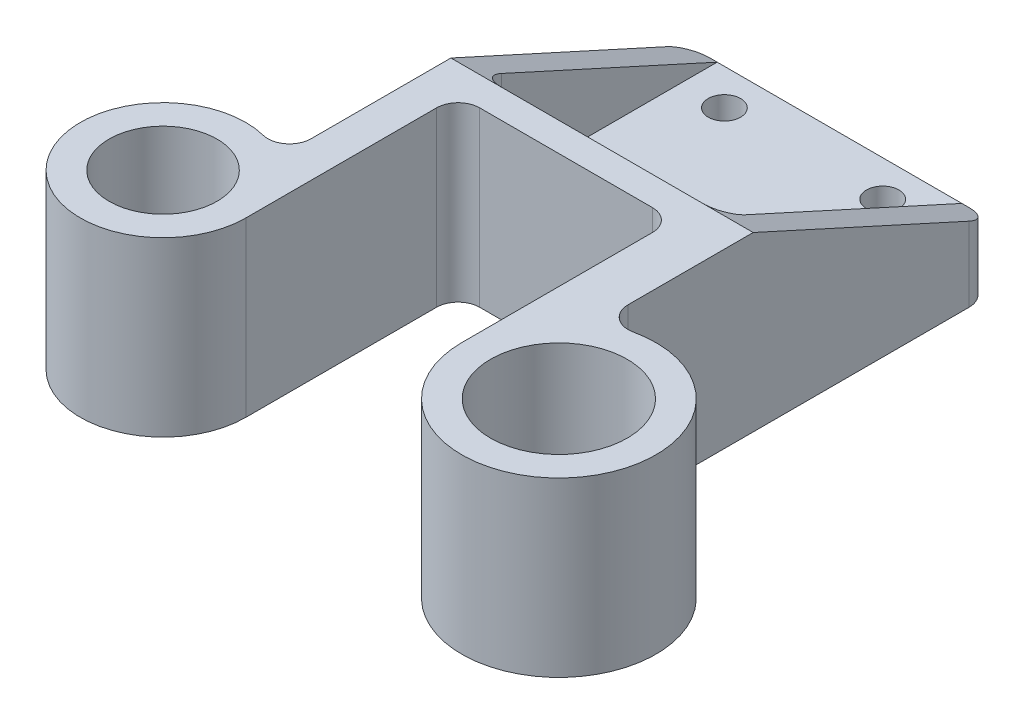
SolidWorks part; units mm, degrees
ref_plane "Front Plane" through (0, 0, 0) normal (0, 0, 1) x (1, 0, 0)
ref_plane "Top Plane" through (0, 0, 0) normal (0, 1, 0) x (1, 0, 0)
ref_plane "Right Plane" through (0, 0, 0) normal (1, 0, 0) x (0, 0, -1)
sketch "Sketch1" plane through (0, 0, 0) normal (0, 1, 0) x (1, 0, 0)
  line L0 (-27.5, 0) -> (27.5, 0) construction
  line L1 (21, 33.5) -> (21, 11.8322)
  line L2 (-11, 38.5) -> (11, 38.5)
  line L3 (-11, 38.5) -> (-11, 61.5)
  line L4 (-11, 61.5) -> (11, 61.5)
  line L5 (11, 38.5) -> (11, 61.5)
  line L6 (-11, 38.5) -> (11, 61.5) construction
  line L7 (-11, 61.5) -> (11, 38.5) construction
  line L8 (-21, 33.5) -> (21, 33.5)
  line L9 (-21, 33.5) -> (-21, 66.5)
  line L10 (-21, 66.5) -> (21, 66.5)
  line L11 (21, 33.5) -> (21, 66.5)
  line L12 (-21, 33.5) -> (21, 66.5) construction
  line L13 (-21, 66.5) -> (21, 33.5) construction
  line L14 (14, 0) -> (14, 33.5)
  line L15 (-16, 0) -> (-16, 33.5)
  line L16 (-21, 33.5) -> (-21, 9.4868)
  line L17 (-16, 29.5) -> (14, 29.5)
  circle A0 centre (27.5, 0) radius 9.5
  circle A1 centre (-27.5, 0) radius 7.5
  circle A2 centre (27.5, 0) radius 13.5
  circle A3 centre (-27.5, 0) radius 11.5
  circle A4 centre (-11, 61.5) radius 2.25
  circle A5 centre (11, 61.5) radius 2.25
  circle A6 centre (11, 38.5) radius 2.25
  circle A7 centre (-11, 38.5) radius 2.25
  point P7 (0, 50)
  point P16 (0, 50)
  dimension "D1" = 15
  dimension "D2" = 19
  dimension "D4" = 4
  dimension "D5" = 4
  dimension "D8" = 4.5
  dimension "D9" = 4.5
  dimension "D10" = 4.5
  dimension "D11" = 4.5
  dimension "D3" = 55
  dimension "D6" = 23
  dimension "D7" = 22
  dimension "D12" = 10
  dimension "D13" = 5
  dimension "D14" = 50
  dimension "D15" = 4
extrude "Boss-Extrude1" add sketch "Sketch1" along normal blind 24 contours A3 A1 | A3 L15 L8 L16 | L8 L11 L10 L9 A7 L3 A4 L4 A5 L5 A6 L2 | A2 A0 | A7 L2 A6 L5 A5 L4 A4 L3 | A2 L1 L8 L14 | L15 L17 L14 L8
sketch "Sketch2" plane through (0, 24, 0) normal (0, 1, 0) x (1, 0, 0)
  line L0 (-21, 66.5) -> (21, 66.5) construction
  line L1 (-17, 66.5) -> (17, 66.5)
  line L2 (-17, 66.5) -> (-17, 33.5)
  line L3 (-17, 33.5) -> (17, 33.5)
  line L4 (17, 66.5) -> (17, 33.5)
  line L5 (-16, 29.5) -> (14, 29.5) construction
  line L6 (-21, 9.4868) -> (-21, 66.5) construction
  line L7 (21, 66.5) -> (21, 11.8322) construction
  dimension "D1" = 4
  dimension "D2" = 4
  dimension "D3" = 4
extrude "Cut-Extrude1" cut sketch "Sketch2" against normal blind 15
sketch "Sketch4" plane through (-17, 0, 0) normal (1, 0, 0) x (0, 0, -1)
  line L0 (33.5, 24) -> (66.5, 9)
  line L1 (66.5, 9) -> (66.5, 24)
  line L2 (66.5, 24) -> (33.5, 24) construction
  line L3 (66.5, 9) -> (66.5, 24) construction
  line L4 (66.5, 24) -> (33.5, 24)
extrude "Cut-Extrude2" cut sketch "Sketch4" against normal through all both and the other way through all
fillet "Fillet1" radius 3 8 edges at (-21, 12, -9.4868) (-21, 4.5, -66.5) (-16, 12, -29.5) (14, 12, -29.5) (21, 12, -11.8322) (21, 4.5, -66.5) (17, 16.5, -33.5) (-17, 16.5, -33.5)
